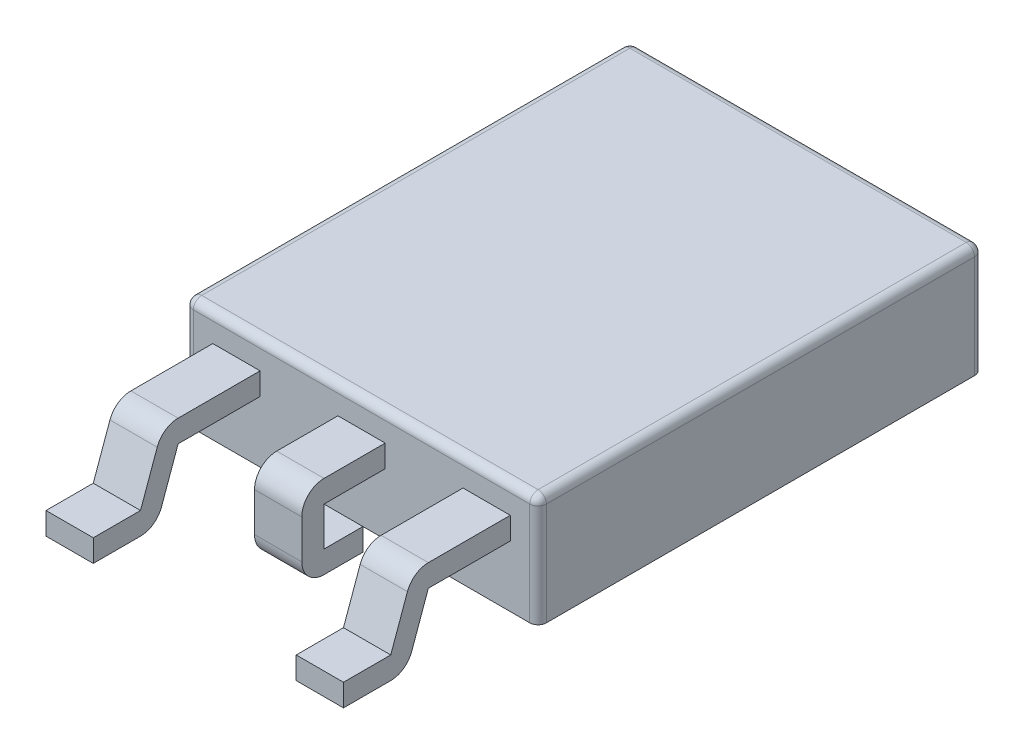
SolidWorks part; units mm, degrees
ref_plane "Front" through (0, 0, 0) normal (0, 0, 1) x (1, 0, 0)
ref_plane "Top" through (0, 0, 0) normal (0, 1, 0) x (1, 0, 0)
ref_plane "Right" through (0, 0, 0) normal (1, 0, 0) x (0, 0, -1)
sketch "Sketch1" plane through (0, 0, 0) normal (0, 1, 0) x (1, 0, 0)
  line L0 (-3.175, -4) -> (3.175, 4) construction
  line L1 (-3.175, 4) -> (3.175, 4)
  line L2 (-3.175, 4) -> (-3.175, -4)
  line L3 (-3.175, -4) -> (3.175, -4)
  line L4 (3.175, 4) -> (3.175, -4)
  point P4 (0, 0)
  dimension "D1" = 6.35
  dimension "D2" = 8
extrude "Boss-Extrude1" add sketch "Sketch1" along normal blind 2
fillet "Fillet1" radius 0.15 8 edges at (0, 2, -4) (3.175, 2, 0) (0, 2, 4) (-3.175, 2, 0) (-3.175, 1, -4) (-3.175, 1, 4) (3.175, 1, -4) (3.175, 1, 4)
sketch "Sketch2" plane through (0, 0, 0) normal (1, 0, 0) x (0, 0, -1)
  line L0 (-4, 1.5) -> (-5.1, 1.5)
  line L1 (-5.5, 1.1) -> (-5.5, 0.4)
  line L2 (-5.1, 0) -> (-4.4, 0)
  line L3 (-4.4, 0) -> (-4.4, 0.4)
  line L4 (-4.4, 0.4) -> (-5.1, 0.4)
  line L5 (-5.1, 0.4) -> (-5.1, 1.1)
  line L6 (-5.1, 1.1) -> (-4, 1.1)
  line L7 (-4, 1.1) -> (-4, 1.5)
  line L8 (-4, 0) -> (-4, 1.85) construction
  line L9 (-3.85, 0) -> (3.85, 0) construction
  arc A0 (-5.1, 1.5) -> (-5.5, 1.1) centre (-5.1, 1.1) ccw
  arc A1 (-5.1, 0) -> (-5.5, 0.4) centre (-5.1, 0.4) cw
  dimension "D3" = 0.4
  dimension "D1" = 1.5
  dimension "D2" = 1.5
  dimension "D4" = 0.4
  dimension "D5" = 0.4
extrude "Boss-Extrude2" add sketch "Sketch2" along normal mid plane 0.85
sketch "Sketch3" plane through (3.175, 0, 0) normal (1, 0, 0) x (0, 0, -1)
  line L0 (-4, 1.5) -> (-5.4735, 1.5)
  line L1 (-5.85, 1.2352) -> (-6.15, 0.4)
  line L2 (-6.15, 0.4) -> (-7, 0.4)
  line L3 (-7, 0.4) -> (-7, 0)
  line L4 (-7, 0) -> (-6.15, 0)
  line L5 (-5.7735, 0.2648) -> (-5.4735, 1.1)
  line L6 (-5.4735, 1.1) -> (-4, 1.1)
  line L7 (-4, 1.1) -> (-4, 1.5) construction
  line L8 (-5.1, 1.1) -> (-4, 1.1) construction
  line L9 (-4, 1.1) -> (-4, 1.5)
  line L10 (-4, 0) -> (-4, 1.85) construction
  arc A0 (-5.4735, 1.5) -> (-5.85, 1.2352) centre (-5.4735, 1.1) ccw
  arc A1 (-6.15, 0) -> (-5.7735, 0.2648) centre (-6.15, 0.4) ccw
  arc A2 (-5.1, 1.5) -> (-5.5, 1.1) centre (-5.1, 1.1) ccw construction
  dimension "D1" = 1.85
  dimension "D2" = 2.15
  dimension "D3" = 3
extrude "Boss-Extrude3" add sketch "Sketch3" against normal blind 0.85 from offset 0.5 offset against normal yes
mirror "Mirror1" about plane through (0, 0, 0) normal (1, 0, 0) of "Boss-Extrude3"
